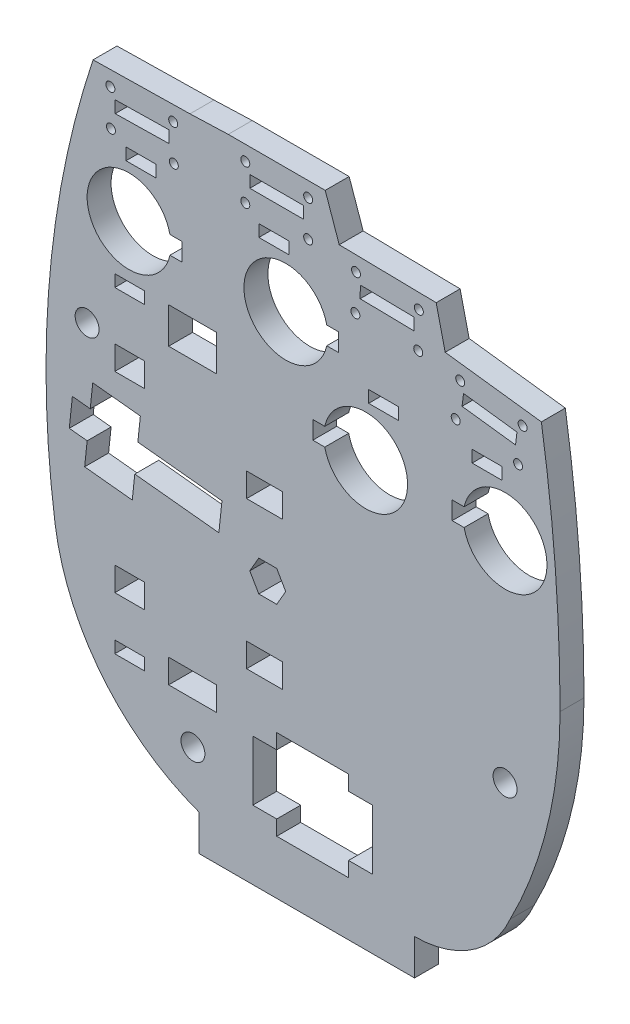
SolidWorks part; units mm, degrees
ref_plane "Front Plane" through (0, 0, 0) normal (0, 0, 1) x (1, 0, 0)
ref_plane "Top Plane" through (0, 0, 0) normal (0, 1, 0) x (1, 0, 0)
ref_plane "Right Plane" through (0, 0, 0) normal (1, 0, 0) x (0, 0, -1)
sketch "Sketch1" plane through (0, 0, 0) normal (0, 0, 1) x (1, 0, 0)
  line L0 (-4.5, 78.51) -> (-4.5, 76.51)
  line L1 (4.5, 78.51) -> (-4.5, 78.51)
  line L2 (-12.9786, -18) -> (-12.9786, -24)
  line L3 (-9.666, 24.0723) -> (-9.153, 28.9531)
  line L4 (-4.5, 76.51) -> (4.5, 76.51)
  line L5 (4.5, 76.51) -> (4.5, 78.51)
  line L6 (-34.6568, 26.6989) -> (-34.1438, 31.5798)
  line L7 (10.3588, 63.1512) -> (10.3588, 60.1512)
  line L8 (-8.1, 82.51) -> (8.1, 82.51)
  line L9 (8.3588, 63.1512) -> (10.3588, 63.1512)
  line L10 (10.4412, 75.8064) -> (26.6388, 75.5236)
  line L11 (32.6473, 57.3216) -> (37.6473, 57.3216)
  line L12 (0, 0) -> (-22.59, 0) construction
  line L13 (10.3588, 60.1512) -> (8.3588, 60.1512)
  line L14 (-17.8416, 63.1512) -> (-15.8416, 63.1512)
  line L15 (-15.8416, 63.1512) -> (-15.8416, 60.1512)
  line L16 (-15.8416, 60.1512) -> (-17.8416, 60.1512)
  line L17 (32.6473, 55.3216) -> (37.6473, 55.3216)
  line L18 (37.6473, 55.3216) -> (37.6473, 57.3216)
  line L19 (32.6473, 57.3216) -> (32.6473, 55.3216)
  line L20 (-27.0195, 78.062) -> (-18.0208, 78.2192)
  line L21 (-27.0195, 78.062) -> (-26.9845, 76.0623)
  line L22 (-10.0543, 52.8756) -> (-18.0543, 52.8756)
  line L23 (-9.153, 28.9531) -> (-23.2041, 30.43)
  line L24 (-26.9845, 76.0623) -> (-17.9858, 76.2195)
  line L25 (-24.1352, 21.571) -> (-32.0914, 22.4072)
  line L26 (-32.0914, 22.4072) -> (-31.6733, 26.3853)
  line L27 (-23.7171, 25.5491) -> (-9.666, 24.0723)
  line L28 (-17.9858, 76.2195) -> (-18.0208, 78.2192)
  line L29 (15.3631, 57.3216) -> (20.3631, 57.3216)
  line L30 (15.3631, 55.3216) -> (20.3631, 55.3216)
  line L31 (-12.9786, -24) -> (23.0214, -24)
  line L32 (20.3631, 55.3216) -> (20.3631, 57.3216)
  line L33 (23.0214, -24) -> (23.0214, -18)
  line L34 (15.3631, 57.3216) -> (15.3631, 55.3216)
  line L35 (-2.9786, 72.1512) -> (2.0214, 72.1512)
  line L36 (13.9709, 71.7441) -> (13.936, 69.7444)
  line L37 (13.936, 69.7444) -> (22.9346, 69.5874)
  line L38 (8.0257, 48.3216) -> (6.0257, 48.3216)
  line L39 (-2.9786, 70.1512) -> (2.0214, 70.1512)
  line L40 (22.9695, 71.5871) -> (13.9709, 71.7441)
  line L41 (6.0257, 48.3216) -> (6.0257, 45.3216)
  line L42 (22.9346, 69.5874) -> (22.9695, 71.5871)
  line L43 (-22.59, 0) -> (-22.59, 82.14) construction
  line L44 (2.0214, 70.1512) -> (2.0214, 72.1512)
  line L45 (18.54, 75.665) -> (18.5934, 78.7251) construction
  line L46 (-2.9786, 72.1512) -> (-2.9786, 70.1512)
  line L47 (40.1436, 63.5476) -> (31.2139, 64.6755)
  line L48 (6.0257, 45.3216) -> (8.0257, 45.3216)
  line L49 (29.3099, 45.3216) -> (31.3099, 45.3216)
  line L50 (29.3099, 48.3216) -> (29.3099, 45.3216)
  line L51 (31.3099, 48.3216) -> (29.3099, 48.3216)
  line L52 (-22.786, 34.408) -> (-30.7422, 35.2443)
  line L53 (31.2139, 64.6755) -> (30.9632, 62.6912)
  line L54 (-25.179, 72.1512) -> (-20.179, 72.1512)
  line L55 (-30.6888, 81.9985) -> (-14.4912, 82.2815)
  line L56 (44.2162, 67.065) -> (28.1438, 69.095)
  line L57 (-25.179, 70.1512) -> (-20.179, 70.1512)
  line L58 (30.9632, 62.6912) -> (39.893, 61.5633)
  line L59 (-20.179, 70.1512) -> (-20.179, 72.1512)
  line L60 (-25.179, 72.1512) -> (-25.179, 70.1512)
  line L61 (39.893, 61.5633) -> (40.1436, 63.5476)
  line L62 (-34.6568, 26.6989) -> (-31.6733, 26.3853)
  line L63 (-4, -2.5) -> (0, -2.5)
  line L64 (12, 0) -> (0, 0)
  line L65 (12, 0) -> (12, -2.5)
  line L66 (12, -15) -> (0, -15)
  line L67 (-30.7422, 35.2443) -> (-31.1603, 31.2662)
  line L68 (-23.2041, 30.43) -> (-22.786, 34.408)
  line L69 (-34.1438, 31.5798) -> (-31.1603, 31.2662)
  line L70 (-24.1352, 21.571) -> (-23.7171, 25.5491)
  line L71 (16, -7.5) -> (38.9913, -7.5) construction
  line L72 (0, -15) -> (0, -12.5)
  line L73 (-4, -12.5) -> (-4, -2.5)
  line L74 (-4, -12.5) -> (0, -12.5)
  line L75 (0, -2.5) -> (0, 0)
  line L76 (0, 0) -> (0, 82.51) construction
  line L77 (-22.0543, 52.8756) -> (-27.0543, 52.8756)
  line L78 (-10.0543, -2.1244) -> (-18.0543, -2.1244)
  line L79 (-22.0543, -2.1244) -> (-27.0543, -2.1244)
  line L80 (0, 0) -> (18.54, 0) construction
  line L81 (16, -12.5) -> (12, -12.5)
  line L82 (16, -12.5) -> (16, -2.5)
  line L83 (16, -2.5) -> (12, -2.5)
  line L84 (12, -12.5) -> (12, -15)
  line L85 (-9.4095, 26.5127) -> (6.8672, 24.8019) construction
  line L86 (0, 23.7547) -> (-3, 23.7547)
  line L87 (-3, 23.7547) -> (-4.5, 21.1566)
  line L88 (-4.5, 21.1566) -> (-3, 18.5585)
  line L89 (18.54, 0) -> (18.54, 75.665) construction
  line L90 (0, 0) -> (36.18, 0) construction
  line L91 (36.18, 0) -> (36.18, 68.08) construction
  line L92 (28.1438, 69.095) -> (26.6388, 75.5236)
  line L93 (10.4412, 75.8064) -> (8.1, 82.51)
  line L94 (-8.1, 82.51) -> (-14.4912, 82.2815)
  line L95 (-34.6568, 26.6989) -> (47.3354, 26.6989) construction
  line L96 (35.6788, 64.1115) -> (36.18, 68.08) construction
  line L97 (-3, 18.5585) -> (0, 18.5585)
  line L98 (0, 18.5585) -> (1.5, 21.1566)
  line L99 (1.5, 21.1566) -> (0, 23.7547)
  line L100 (0, 18.5585) -> (-3, 23.7547) construction
  line L101 (0, 23.7547) -> (-3, 18.5585) construction
  line L102 (38.1473, 11.8216) -> (-37.0527, 11.8216) construction
  line L103 (-27.7956, 79.5486) -> (-30.6451, 79.4989) construction
  line L104 (0.9634, 10.717) -> (0.9634, 6.717)
  line L105 (0.9634, 6.717) -> (-5.0366, 6.717)
  line L106 (-5.0366, 6.717) -> (-5.0366, 10.717)
  line L107 (-5.0366, 10.717) -> (0.9634, 10.717)
  line L108 (-5.0366, 31.3356) -> (0.9634, 31.3356)
  line L109 (-5.0366, 35.3356) -> (-5.0366, 31.3356)
  line L110 (0.9634, 35.3356) -> (-5.0366, 35.3356)
  line L111 (0.9634, 31.3356) -> (0.9634, 35.3356)
  line L112 (-30.6451, 79.4989) -> (-30.6888, 81.9985) construction
  line L113 (-17.2971, 79.732) -> (-14.4475, 79.7819) construction
  line L114 (-14.4475, 79.7819) -> (-14.4912, 82.2815) construction
  line L115 (-22.5201, 78.1406) -> (-22.59, 82.14) construction
  line L116 (5.25, 80.01) -> (8.1, 80.01) construction
  line L117 (8.1, 80.01) -> (8.1, 82.51) construction
  line L118 (-5.25, 80.01) -> (-8.1, 80.01) construction
  line L119 (-22.0543, -0.1244) -> (-27.0543, -0.1244)
  line L120 (-8.1, 80.01) -> (-8.1, 82.51) construction
  line L121 (-10.0543, 1.8756) -> (-10.0543, -2.1244)
  line L122 (30.6581, 66.2576) -> (27.8306, 66.6147) construction
  line L123 (-10.0543, 52.8756) -> (-10.0543, 46.8756)
  line L124 (-10.0543, 1.8756) -> (-18.0543, 1.8756)
  line L125 (-18.0543, 1.8756) -> (-18.0543, -2.1244)
  line L126 (27.8306, 66.6147) -> (28.1438, 69.095) construction
  line L127 (13.2472, 73.257) -> (10.3976, 73.3067) construction
  line L128 (-22.0543, -0.1244) -> (-22.0543, -2.1244)
  line L129 (-27.0543, -0.1244) -> (-27.0543, -2.1244)
  line L130 (30.6581, 66.2576) -> (29.9062, 60.3049) construction
  line L131 (-10.0543, 46.8756) -> (-18.0543, 46.8756)
  line L132 (-27.0543, 52.8756) -> (-27.0543, 50.8756)
  line L133 (-18.0543, 46.8756) -> (-18.0543, 52.8756)
  line L134 (10.4412, 75.8064) -> (10.3976, 73.3067) construction
  line L135 (-22.0543, 6.717) -> (-22.0543, 10.717)
  line L136 (-22.0543, 10.717) -> (-27.0543, 10.717)
  line L137 (-27.0543, 50.8756) -> (-22.0543, 50.8756)
  line L138 (-22.0543, 52.8756) -> (-22.0543, 50.8756)
  line L139 (-27.0543, 10.717) -> (-27.0543, 6.717)
  line L140 (-27.0543, 6.717) -> (-22.0543, 6.717)
  line L141 (-27.0543, 38.7272) -> (-22.0543, 38.7272)
  line L142 (-22.0543, 38.7272) -> (-22.0543, 42.7272)
  line L143 (-22.0543, 42.7272) -> (-27.0543, 42.7272)
  line L144 (-27.0543, 42.7272) -> (-27.0543, 38.7272)
  line L145 (23.7456, 73.0738) -> (26.5951, 73.024) construction
  line L146 (26.5951, 73.024) -> (26.6388, 75.5236) construction
  line L147 (41.0753, 64.9418) -> (43.9029, 64.5847) construction
  line L148 (41.0753, 64.9418) -> (40.3235, 58.9891) construction
  line L149 (40.3235, 58.9891) -> (43.151, 58.632) construction
  line L150 (43.151, 58.632) -> (43.9029, 64.5847) construction
  line L151 (23.7456, 73.0738) -> (23.6409, 67.0747) construction
  line L152 (13.2472, 73.257) -> (13.1425, 67.2579) construction
  line L153 (-17.2971, 79.732) -> (-17.1923, 73.733) construction
  line L154 (-27.7956, 79.5486) -> (-27.6908, 73.5496) construction
  line L155 (38.1473, 46.8216) -> (38.1473, 11.8216) construction
  arc A0 (-37.0527, 11.8216) -> (-30.6888, 81.9985) centre (116.3395, 33.2885) cw
  circle A1 centre (-1.5, 21.1566) radius 4.5 construction
  arc A2 (8.3588, 63.1512) -> (8.3588, 60.1512) centre (1.5214, 61.6512) ccw
  arc A3 (8.0257, 45.3216) -> (8.0257, 48.3216) centre (14.8631, 46.8216) ccw
  arc A4 (-17.8416, 63.1512) -> (-17.8416, 60.1512) centre (-24.679, 61.6512) ccw
  arc A5 (31.3099, 45.3216) -> (31.3099, 48.3216) centre (38.1473, 46.8216) ccw
  arc A6 (23.0214, -18) -> (38.9913, -7.5) centre (23.0214, -0.6053) ccw
  arc A7 (47.3354, 26.6989) -> (38.9913, -7.5) centre (-26.9196, 26.6989) cw
  arc A8 (-37.0527, 11.8216) -> (-12.9786, -18) centre (-0.147, 16.9865) ccw
  arc A9 (47.3354, 26.6989) -> (44.2162, 67.065) centre (-215.4084, 26.6989) ccw
  circle A11 centre (38.1473, 11.8216) radius 2
  circle A12 centre (-14, -9.1244) radius 2
  circle A18 centre (-5.25, 80.01) radius 0.75
  circle A22 centre (-31.6815, 43.4564) radius 2
  circle A49 centre (5.25, 80.01) radius 0.75
  circle A50 centre (5.25, 74.01) radius 0.75
  circle A51 centre (-5.25, 74.01) radius 0.75
  circle A52 centre (-27.7956, 79.5486) radius 0.75
  circle A53 centre (-17.2971, 79.732) radius 0.75
  circle A54 centre (-27.6908, 73.5496) radius 0.75
  circle A55 centre (-17.1923, 73.733) radius 0.75
  circle A56 centre (23.6409, 67.0747) radius 0.75
  circle A57 centre (13.1425, 67.2579) radius 0.75
  circle A58 centre (23.7456, 73.0738) radius 0.75
  circle A59 centre (13.2472, 73.257) radius 0.75
  circle A60 centre (29.9062, 60.3049) radius 0.7496
  circle A61 centre (41.0753, 64.9418) radius 0.7496
  circle A62 centre (30.6581, 66.2576) radius 0.7496
  circle A63 centre (40.3235, 58.9891) radius 0.7496
  dimension "D1" = 4
  dimension "D2" = 1.5
  dimension "D11" = 1.5214
  dimension "D12" = 2.0214
  dimension "D16" = 6.0257
  dimension "D17" = 4
  dimension "D18" = 8.3588
  dimension "D19" = 22.59
  dimension "D22" = 4
  dimension "D23" = 18.54
  dimension "D24" = 75.665
  dimension "D25" = 12
  dimension "D35" = 4
  dimension "D36" = 16.2
  dimension "D37" = 2
  dimension "D38" = 29.3099
  dimension "D39" = 2.85
  dimension "D40" = 46.8216
  dimension "D43" = 2.85
  dimension "D44" = 24.679
  dimension "D45" = 9
  dimension "D46" = 0.7292
  dimension "D47" = 4.9078
  dimension "D49" = 5.0366
  dimension "D51" = 9.666
  dimension "D55" = 24
  dimension "D56" = 15.8416
  dimension "D13" = 4
  dimension "D58" = 2.5
  dimension "D59" = 18.0543
  dimension "D60" = 8.1
  dimension "D61" = 6
  dimension "D63" = 22.0543
  dimension "D64" = 2.5
  dimension "D65" = 2.85
  dimension "D52" = 10.0543
  dimension "D48" = 25.1285
  dimension "D53" = 12.9786
  dimension "D57" = 4
  dimension "D69" = 6
  dimension "D70" = 2.5
  dimension "D71" = 1.8756
  dimension "D79" = 43.4564
  dimension "D82" = 55.3216
  dimension "D67" = 2.5
  dimension "D68" = 31.6815
  dimension "D5" = 7
  dimension "D29" = 2.5
  dimension "D83" = 8.1
  dimension "D85" = 2
  dimension "D10" = 0.9634
  dimension "D14" = 82.51
  dimension "D15" = 3
  dimension "D20" = 10
  dimension "D21" = 82.14
  dimension "D26" = 15.3631
  dimension "D27" = 2.5
  dimension "D28" = 0
  dimension "D30" = 20.3631
  dimension "D31" = 36.18
  dimension "D32" = 68.08
  dimension "D33" = 23.0214
  dimension "D34" = 6
  dimension "D41" = 14.8631
  dimension "D42" = 32.6473
  dimension "D50" = 9.153
  dimension "D54" = 14
  dimension "D62" = 20.179
  dimension "D66" = 2.85
  dimension "D72" = 6.717
  dimension "D73" = 9.0001
  dimension "D74" = 9.0007
  dimension "D75" = 35
  dimension "D76" = 21.571
  dimension "D77" = 31.3356
  dimension "D78" = 6
  dimension "D80" = 45.3216
  dimension "D81" = 46.8756
  dimension "D84" = 60.1512
  dimension "D86" = 70.1512
  dimension "D93" = 9.1244
extrude "Boss-Extrude1" add sketch "Sketch1" along normal blind 4
equation "\"D14@Sketch1\"= \"HL@parametersSketch@prostheticParameters.SLDPRT\" * 0.446'Mioddle Base Frame "
equation "\"D19@Sketch1\"= \"HB@parametersSketch@prostheticParameters.SLDPRT\" * 0.251'Index Base Frame X"
equation "\"D21@Sketch1\"= \"HL@parametersSketch@prostheticParameters.SLDPRT\" * 0.444'Index Base Frame Y"
equation "\"D23@Sketch1\"= \"HB@parametersSketch@prostheticParameters.SLDPRT\" * 0.206'Ring Base Frame X"
equation "\"D24@Sketch1\"= \"HL@parametersSketch@prostheticParameters.SLDPRT\" * 0.409'Ring Base Frame Y"
equation "\"D31@Sketch1\"= \"HB@parametersSketch@prostheticParameters.SLDPRT\" * 0.402'Pinky Base Frame X"
equation "\"D32@Sketch1\"= \"HL@parametersSketch@prostheticParameters.SLDPRT\" * 0.368'Pinky Base Frame Y"
equation "\"D36@Sketch1\"= \"fingerWidth@parametersSketch@prostheticParameters.SLDPRT\"'Fingers Width"
equation "\"D76@Sketch1\"= \"HL@parametersSketch@prostheticParameters.SLDPRT\" * 0.1166'Hole Thumb Y"
equation "\"D51@Sketch1\"= \"HB@parametersSketch@prostheticParameters.SLDPRT\" * 0.1074'Hole Thumb X1"
equation "\"D50@Sketch1\" = \"HB@parametersSketch@prostheticParameters.SLDPRT\" * 0.1017'Hole Thumb X2"
equation "\"D73@Sketch1\"= \"fingerWidth@parametersSketch@prostheticParameters.SLDPRT\" * 0.55556"
equation "\"D74@Sketch1\"= \"fingerWidth@parametersSketch@prostheticParameters.SLDPRT\" * 0.5556"
equation "\"D60@Sketch1\"= \"fingerWidth@parametersSketch@prostheticParameters.SLDPRT\" / 2"
equation "\"D83@Sketch1\"= \"fingerWidth@parametersSketch@prostheticParameters.SLDPRT\" / 2"
